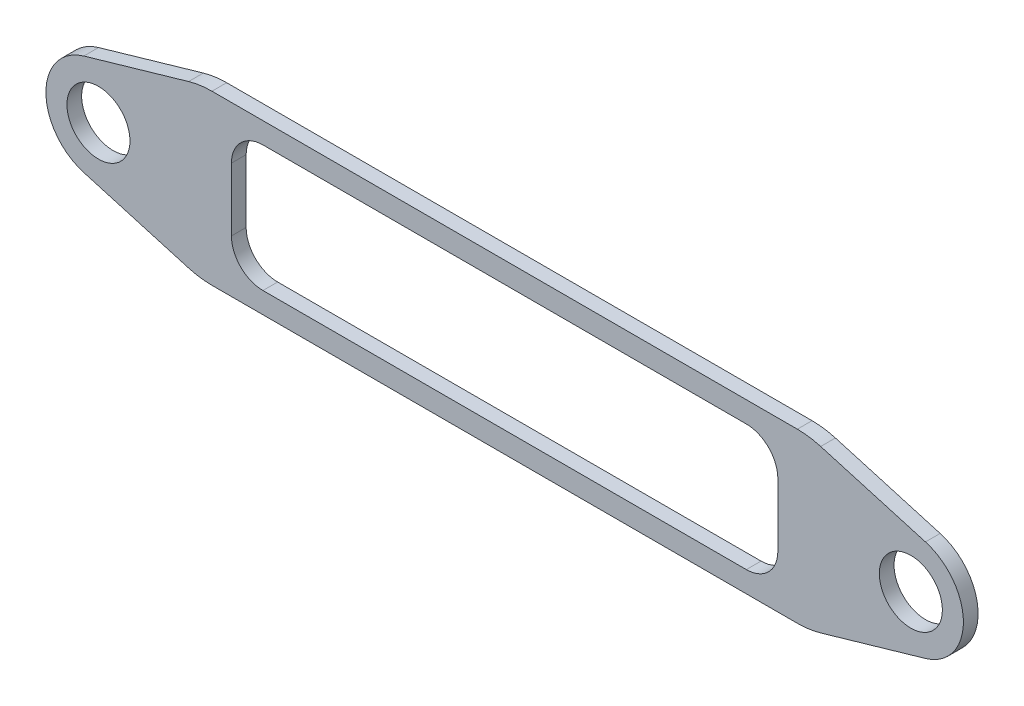
SolidWorks part; units mm, degrees
ref_plane "Front Plane" through (0, 0, 0) normal (0, 0, 1) x (1, 0, 0)
ref_plane "Top Plane" through (0, 0, 0) normal (0, 1, 0) x (1, 0, 0)
ref_plane "Right Plane" through (0, 0, 0) normal (1, 0, 0) x (0, 0, -1)
sketch "Sketch1" plane through (0, 0, 0) normal (0, 0, 1) x (1, 0, 0)
  line L0 (7.6491, -0.6064) -> (7.6491, 0.8936)
  line L1 (6.8991, 1.6436) -> (-4.6009, 1.6436)
  line L2 (-5.8148, -1.8564) -> (8.113, -1.8564)
  line L3 (8.6685, -1.7777) -> (11.1606, -1.0572)
  line L4 (11.1606, 1.3445) -> (8.6685, 2.065)
  line L5 (8.113, 2.1436) -> (-5.8148, 2.1436)
  line L6 (-6.3703, 2.065) -> (-8.8624, 1.3445)
  line L7 (-8.8624, -1.0572) -> (-6.3703, -1.7777)
  line L8 (-5.3509, 0.8936) -> (-5.3509, -0.6064)
  line L9 (-4.6009, -1.3564) -> (6.8991, -1.3564)
  arc A0 (8.113, -1.8564) -> (8.6685, -1.7777) centre (8.113, 0.1436) ccw
  arc A1 (11.1606, -1.0572) -> (11.1606, 1.3445) centre (10.8134, 0.1436) ccw
  arc A2 (8.6685, 2.065) -> (8.113, 2.1436) centre (8.113, 0.1436) ccw
  arc A3 (-5.8148, 2.1436) -> (-6.3703, 2.065) centre (-5.8148, 0.1436) ccw
  arc A4 (-8.8624, 1.3445) -> (-8.8624, -1.0572) centre (-8.5152, 0.1436) ccw
  arc A5 (-6.3703, -1.7777) -> (-5.8148, -1.8564) centre (-5.8148, 0.1436) ccw
  arc A6 (6.8991, -1.3564) -> (7.6491, -0.6064) centre (6.8991, -0.6064) ccw
  arc A7 (7.6491, 0.8936) -> (6.8991, 1.6436) centre (6.8991, 0.8936) ccw
  arc A8 (-4.6009, 1.6436) -> (-5.3509, 0.8936) centre (-4.6009, 0.8936) ccw
  arc A9 (-5.3509, -0.6064) -> (-4.6009, -1.3564) centre (-4.6009, -0.6064) ccw
  circle A10 centre (-8.5152, 0.1436) radius 0.75
  circle A11 centre (10.8134, 0.1436) radius 0.75
extrude "Boss-Extrude1" add sketch "Sketch1" along normal blind 0.35
